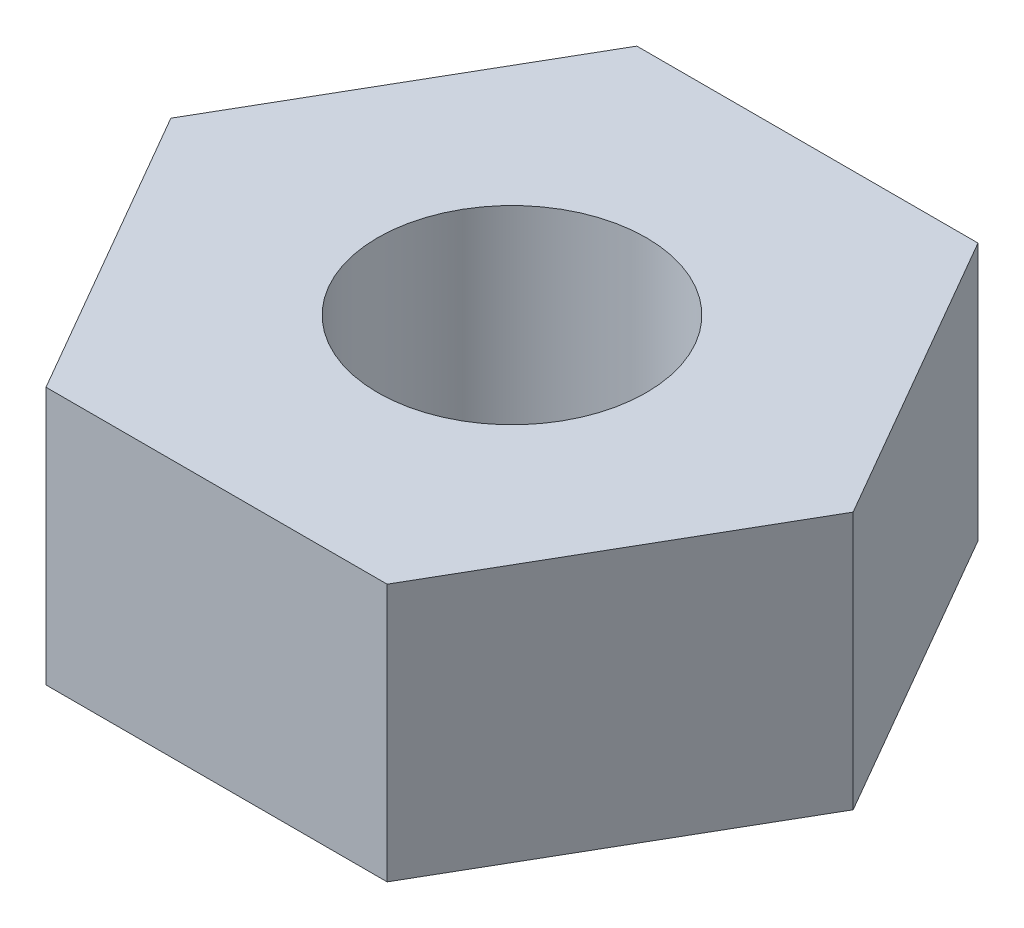
SolidWorks part; units mm, degrees
material "acero"
ref_plane "Alzado" through (0, 0, 0) normal (0, 0, 1) x (1, 0, 0)
ref_plane "Planta" through (0, 0, 0) normal (0, 1, 0) x (1, 0, 0)
ref_plane "Vista lateral" through (0, 0, 0) normal (1, 0, 0) x (0, 0, -1)
sketch "Croquis1" plane through (0, 0, 0) normal (0, 1, 0) x (1, 0, 0)
  line L1 (-1.5877, 2.75) -> (-3.1754, 0)
  line L2 (-3.1754, 0) -> (-1.5877, -2.75)
  line L3 (-1.5877, -2.75) -> (1.5877, -2.75)
  line L4 (1.5877, -2.75) -> (3.1754, 0)
  line L5 (3.1754, 0) -> (1.5877, 2.75)
  line L6 (1.5877, 2.75) -> (-1.5877, 2.75)
  circle A0 centre (0, 0) radius 2.75 construction
  circle A1 centre (0, 0) radius 1.25
  dimension "D1" = 2.5
  dimension "D2" = 5.5
extrude "Saliente-Extruir1" add sketch "Croquis1" along normal blind 2.4
